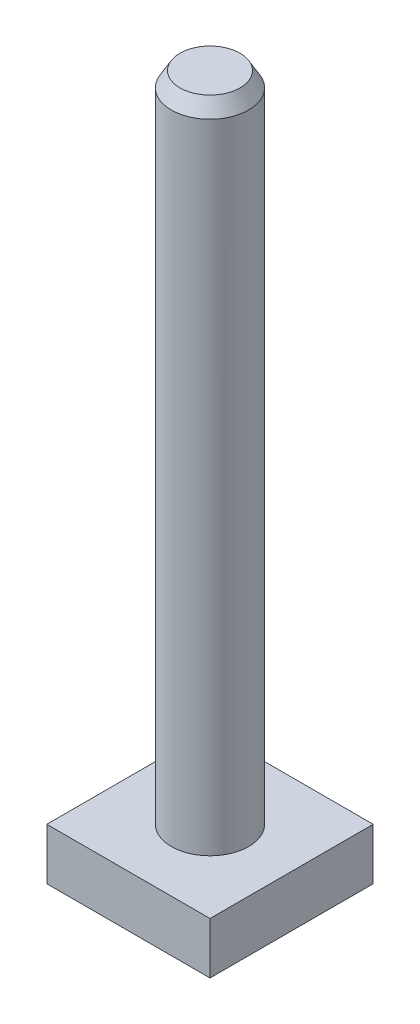
SolidWorks part; units mm, degrees
ref_plane "Front Plane" through (0, 0, 0) normal (0, 0, 1) x (1, 0, 0)
ref_plane "Top Plane" through (0, 0, 0) normal (0, 1, 0) x (1, 0, 0)
ref_plane "Right Plane" through (0, 0, 0) normal (1, 0, 0) x (0, 0, -1)
sketch "Sketch1" plane through (0, 0, 0) normal (0, 0, 1) x (1, 0, 0)
  line L0 (0, 0) -> (0, 101.2574) construction
  line L1 (0, 0) -> (4.5, 0)
  line L2 (4.5, 0) -> (4.5, 76)
  line L3 (4.5, 76) -> (0, 76)
  line L4 (0, 76) -> (0, 0)
  dimension "D1" = 76
  dimension "D2" = 4.5
revolve "Revolve1" add sketch "Sketch1" angle 360 about L0
sketch "Sketch2" plane through (0, 0, 0) normal (0, 1, 0) x (1, 0, 0)
  line L1 (-9.5, 9.5) -> (9.5, 9.5)
  line L2 (-9.5, 9.5) -> (-9.5, -9.5)
  line L3 (-9.5, -9.5) -> (9.5, -9.5)
  line L4 (9.5, 9.5) -> (9.5, -9.5)
  line L5 (-9.5, 9.5) -> (9.5, -9.5) construction
  line L6 (-9.5, -9.5) -> (9.5, 9.5) construction
  point P0 (0, 0)
  dimension "D1" = 19
extrude "Boss-Extrude1" add sketch "Sketch2" against normal blind 6
chamfer "Chamfer2" distance 1 angle 60 1 edges at (0, 76, -4.5)
